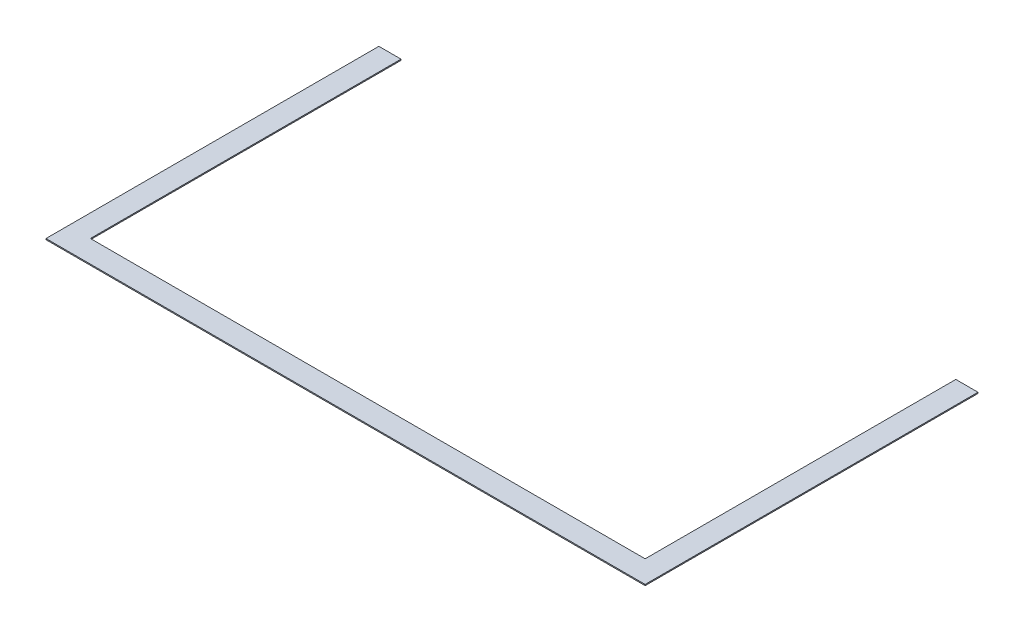
SolidWorks part; units mm, degrees
ref_plane "Front Plane" through (0, 0, 0) normal (0, 0, 1) x (1, 0, 0)
ref_plane "Top Plane" through (0, 0, 0) normal (0, 1, 0) x (1, 0, 0)
ref_plane "Right Plane" through (0, 0, 0) normal (1, 0, 0) x (0, 0, -1)
sketch "Sketch1" plane through (0, 0, 0) normal (0, 1, 0) x (1, 0, 0)
  line L1 (-106.6212, -63.3788) -> (2593.3788, -63.3788)
  line L2 (-106.6212, -63.3788) -> (-106.6212, 1436.6212)
  line L3 (-106.6212, 1436.6212) -> (-6.6212, 1436.6212)
  line L4 (2593.3788, -63.3788) -> (2593.3788, 1436.6212)
  line L6 (2493.3788, 186.6212) -> (2493.3788, 1436.6212)
  line L7 (-6.6212, 36.6212) -> (2493.3788, 36.6212)
  line L10 (2493.3788, 36.6212) -> (2493.3788, 186.6212)
  line L12 (2493.3788, 1436.6212) -> (2593.3788, 1436.6212)
  line L13 (-6.6212, 36.6212) -> (-6.6212, 1436.6212)
  point P0 (0, 0)
  point P6 (-101.6212, 101.6212)
  dimension "D2" = 1500
  dimension "D3" = 2500
  dimension "D4" = 100
  dimension "D6" = 100
extrude "Boss-Extrude1" add sketch "Sketch1" along normal blind 5
